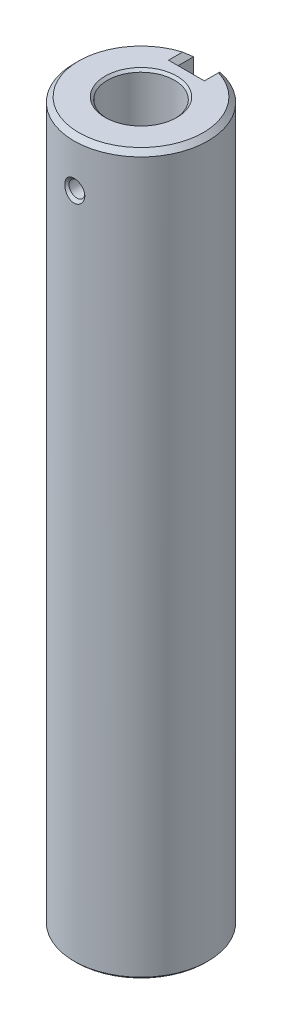
SolidWorks part; units mm, degrees
ref_plane "Plan de face" through (0, 0, 0) normal (0, 0, 1) x (1, 0, 0)
ref_plane "Plan de dessus" through (0, 0, 0) normal (0, 1, 0) x (1, 0, 0)
ref_plane "Plan de droite" through (0, 0, 0) normal (1, 0, 0) x (0, 0, -1)
sketch "Esquisse1" plane through (0, 0, 0) normal (0, 1, 0) x (1, 0, 0)
  circle A0 centre (0, 0) radius 14
extrude "Boss.-Extru.1" add sketch "Esquisse1" along normal blind 150
chamfer "Chanfrein1" distance 1 angle 45 1 edges at (0, 150, 14)
sketch "Esquisse2" plane through (0, 150, 0) normal (0, 1, 0) x (-1, 0, 0)
  point P0 (0, 0)
hole_wizard "Diamètre du perçage Ø14.0 (14)1" positions "Esquisse5" profile "Esquisse4" hole size "Ø14.0" standard "ISO"
sketch "Esquisse5" plane through (0, 150, 0) normal (0, 1, 0) x (-1, 0, 0)
  point P0 (0, 0)
sketch "Esquisse4" plane through (0, 150, 0) normal (1, 0, 0) x (0, 0, 1)
  line L0 (0, 0) -> (0, 39.206)
  line L1 (0, 39.206) -> (7, 35)
  line L2 (7, 35) -> (7, 0.5)
  line L3 (7, 0.5) -> (7.5, 0)
  line L5 (7.5, 0) -> (0, 0)
  line L6 (-7, 0.5) -> (-7.5, 0) construction
  line L10 (0, 39.206) -> (-7, 35) construction
  line L11 (0, -6.35) -> (0, 107.95) construction
  dimension "Diamètre du perçage" = 14
  dimension "Profondeur du perçage" = 35
  dimension "Diamètre du fraisage entrant" = 15
  dimension "Angle du fraisage entrant" = 90
  dimension "Angle de pointe" = 118
chamfer "Chanfrein2" distance 0.5 angle 45 1 edges at (0, 0, 14)
hole_wizard "Trou taraudé M8x1.01" positions "Esquisse7" profile "Esquisse6" tap size "M8x1.0" standard "ISO"
sketch "Esquisse7" plane through (0, 0, 0) normal (0, -1, 0) x (1, 0, 0)
  point P0 (0, 0)
sketch "Esquisse6" plane through (0, 0, 0) normal (1, 0, 0) x (0, 0, -1)
  line L0 (0, 0) -> (0, 27.103)
  line L1 (0, 27.103) -> (3.5, 25)
  line L2 (3.5, 25) -> (3.5, 0)
  line L5 (3.5, 0) -> (0, 0)
  line L10 (0, 27.103) -> (-3.5, 25) construction
  line L11 (0, -6.35) -> (0, 107.95) construction
  dimension "Diamètre du trou pour taraudage" = 7
  dimension "Profondeur du trou pour taraudage" = 25
  dimension "Angle de pointe" = 118
cosmetic thread "Filetage de perçage1" parameters "D1"=20, "D2"=8
sketch "Esquisse8" plane through (0, 0, 0) normal (0, 0, 1) x (1, 0, 0)
  line L1 (0, 146.238) -> (0, 132.6328) construction
  line L2 (7.5, 140) -> (-7.5, 140)
  line L3 (7.5, 140) -> (-7.5, 140) construction
  point P5 (0, 140)
  dimension "D1" = 10
hole_wizard "Trou taraudé M42" positions "Esquisse12" profile "Esquisse11" tap size "M4" standard "ISO" end condition up to next
sketch "Esquisse12" plane through (0, 0, 0) normal (0, 0, 1) x (1, 0, 0)
  point P0 (0, 140)
sketch "Esquisse11" plane through (0, 140, 0) normal (1, 0, 0) x (0, 1, 0)
  line L0 (0, 0) -> (0, 14)
  line L1 (0, 14) -> (2.25, 14)
  line L2 (1.65, 13.4) -> (1.65, 0)
  line L5 (1.65, 0) -> (0, 0)
  line L7 (2.25, 14) -> (1.65, 13.4)
  line L8 (-2.25, 14) -> (-1.65, 13.4) construction
  line L11 (0, -6.35) -> (0, 107.95) construction
  dimension "Diamètre du trou pour taraudage jusqu'au prochain" = 3.3
  dimension "Profondeur du trou pour taraudage jusqu'au prochain" = 14
  dimension "Diamètre du fraisage débouchant" = 4.5
  dimension "Angle du fraisage débouchant" = 90
cosmetic thread "Filetage de perçage2" parameters "D2"=4
sketch "Esquisse13" plane through (0, 150, 0) normal (0, 1, 0) x (-1, 0, 0)
  line L0 (0, -14.6028) -> (0, -5.0087) construction
  line L1 (0, -14) -> (6.79, -14) construction
  line L2 (2.75, -14.6028) -> (2.75, -10.5)
  line L3 (-2.75, -14.6028) -> (-2.75, -10.5)
  line L4 (-2.75, -10.5) -> (2.75, -10.5)
  line L5 (0, -10.5) -> (6.79, -10.5) construction
  line L6 (2.75, -14.6028) -> (-2.75, -14.6028)
  line L9 (2.75, -14.6028) -> (2.75, -5.0087) construction
  line L10 (-2.75, -14.6028) -> (-2.75, -5.0087) construction
  circle A0 centre (0, 0) radius 14 construction
  dimension "D1" = 2.75
  dimension "D2" = 2.75
  dimension "D3" = 3.5
extrude "Enlèv. mat.-Extru.1" cut sketch "Esquisse13" against normal up to next
chamfer "Chanfrein3" distance 1 angle 45 3 edges at (2.75, 0, -11.8585) (-2.75, 0, -11.8585) (0, 0, -10.5)
chamfer "Chanfrein4" distance 1 angle 45 3 edges at (2.75, 150, -11.6029) (-2.75, 150, -11.6029) (0, 150, -10.5)
